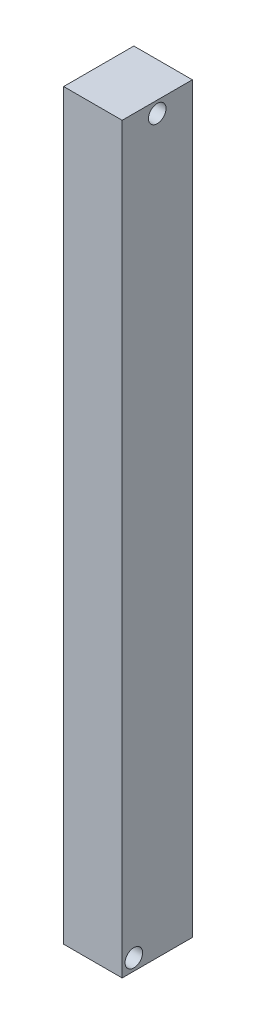
SolidWorks part; units mm, degrees
ref_plane "Front Plane" through (0, 0, 0) normal (0, 0, 1) x (1, 0, 0)
ref_plane "Top Plane" through (0, 0, 0) normal (0, 1, 0) x (1, 0, 0)
ref_plane "Right Plane" through (0, 0, 0) normal (1, 0, 0) x (0, 0, -1)
sketch "Sketch1" plane through (0, 0, 0) normal (0, 1, 0) x (1, 0, 0)
  line L1 (0, 0) -> (127, 0)
  line L2 (0, 0) -> (0, 152.4)
  line L3 (0, 152.4) -> (127, 152.4)
  line L4 (127, 0) -> (127, 152.4)
  dimension "D1" = 152.4
  dimension "D2" = 127
extrude "Boss-Extrude2" add sketch "Sketch1" along normal blind 1612.9
sketch "Sketch2" plane through (127, 0, 0) normal (1, 0, 0) x (0, 0, -1)
  line L0 (0, 0) -> (152.4, 0) construction
  line L1 (0, 1612.9) -> (0, 0) construction
  circle A0 centre (25.4, 25.4) radius 19.05
  dimension "D1" = 38.1
  dimension "D2" = 25.4
  dimension "D3" = 25.4
extrude "Cut-Extrude1" cut sketch "Sketch2" against normal blind 152.4
sketch "Sketch3" plane through (127, 0, 0) normal (1, 0, 0) x (0, 0, -1)
  line L0 (0, 1612.9) -> (152.4, 1612.9) construction
  line L2 (152.4, 1612.9) -> (152.4, 0) construction
  circle A0 centre (76.2, 1587.5) radius 19.05
  dimension "D1" = 25.4
  dimension "D2" = 76.2
  dimension "D3" = 38.1
extrude "Cut-Extrude2" cut sketch "Sketch3" against normal blind 152.4
